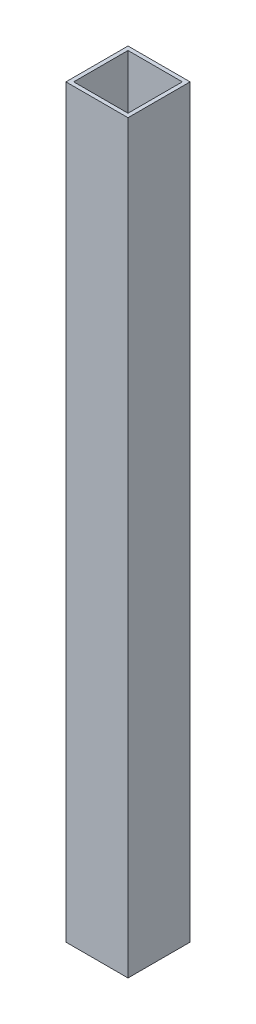
SolidWorks part; units mm, degrees
material "6061 Alloy"
ref_plane "Front Plane" through (0, 0, 0) normal (0, 0, 1) x (1, 0, 0)
ref_plane "Top Plane" through (0, 0, 0) normal (0, 1, 0) x (1, 0, 0)
ref_plane "Right Plane" through (0, 0, 0) normal (1, 0, 0) x (0, 0, -1)
sketch "Sketch1" plane through (0, 0, 0) normal (0, 1, 0) x (1, 0, 0)
  line L1 (-11.1125, -11.1125) -> (11.1125, -11.1125)
  line L2 (-11.1125, -11.1125) -> (-11.1125, 11.1125)
  line L3 (-11.1125, 11.1125) -> (11.1125, 11.1125)
  line L4 (11.1125, -11.1125) -> (11.1125, 11.1125)
  line L5 (-11.1125, -11.1125) -> (11.1125, 11.1125) construction
  line L6 (-11.1125, 11.1125) -> (11.1125, -11.1125) construction
  line L7 (-12.7, -12.7) -> (12.7, -12.7)
  line L8 (-12.7, -12.7) -> (-12.7, 12.7)
  line L9 (-12.7, 12.7) -> (12.7, 12.7)
  line L10 (12.7, -12.7) -> (12.7, 12.7)
  line L11 (-12.7, -12.7) -> (12.7, 12.7) construction
  line L12 (-12.7, 12.7) -> (12.7, -12.7) construction
  point P0 (0, 0)
  point P6 (0, 0)
  dimension "D1" = 25.4
  dimension "D2" = 1.5875
extrude "Boss-Extrude1" add sketch "Sketch1" along normal blind 304.8
